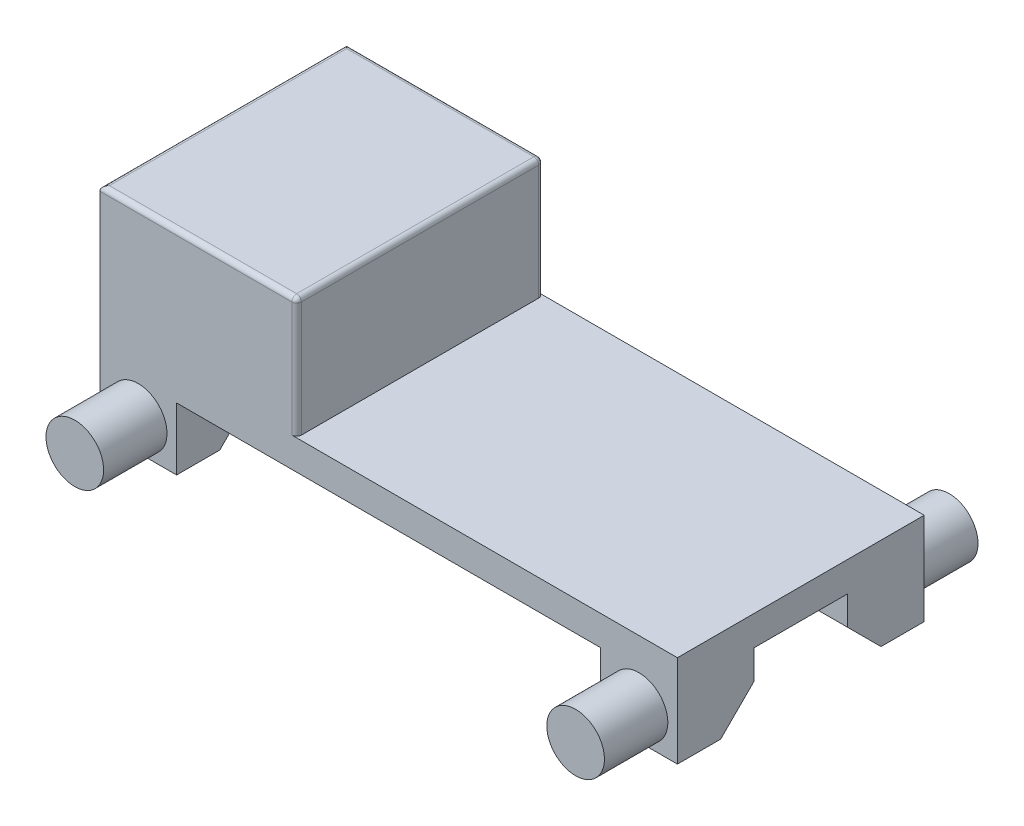
SolidWorks part; units mm, degrees
material "ФФ201"
ref_plane "Спереди" through (0, 0, 0) normal (0, 0, 1) x (1, 0, 0)
ref_plane "Сверху" through (0, 0, 0) normal (0, 1, 0) x (1, 0, 0)
ref_plane "Справа" through (0, 0, 0) normal (1, 0, 0) x (0, 0, -1)
sketch "Эскиз1" plane through (0, 0, 0) normal (0, 1, 0) x (1, 0, 0)
  line L1 (-601.5, -257) -> (601.5, -257)
  line L2 (-601.5, -257) -> (-601.5, 257)
  line L3 (-601.5, 257) -> (601.5, 257)
  line L4 (601.5, -257) -> (601.5, 257)
  line L5 (-601.5, -257) -> (601.5, 257) construction
  line L6 (-601.5, 257) -> (601.5, -257) construction
  point P0 (0, 0)
  dimension "D1" = 1203
  dimension "D2" = 514
extrude "Бобышка-Вытянуть1" add sketch "Эскиз1" along normal blind 62
sketch "Эскиз2" plane through (0, 62, 0) normal (0, 1, 0) x (1, 0, 0)
  line L0 (-601.5, -257) -> (601.5, -257) construction
  line L1 (-601.5, 257) -> (-191.5, 257)
  line L2 (-601.5, 257) -> (-601.5, -257)
  line L3 (-601.5, -257) -> (-191.5, -257)
  line L4 (-191.5, 257) -> (-191.5, -257)
  dimension "D1" = 410
extrude "Бобышка-Вытянуть2" add sketch "Эскиз2" along normal blind 250
fillet "Скругление1" radius 10 6 edges at (-191.5, 187, -257) (-191.5, 187, 257) (-191.5, 312, 0) (-396.5, 312, -257) (-601.5, 312, 0) (-396.5, 312, 257)
sketch "Эскиз3" plane through (0, 0, 0) normal (0, -1, 0) x (1, 0, 0)
  line L0 (171.6, 0) -> (-171.6, 0) construction
  line L1 (-601.5, 257) -> (-441.5, 257)
  line L2 (-601.5, 257) -> (-601.5, 97)
  line L3 (-601.5, 97) -> (-441.5, 97)
  line L4 (-441.5, 257) -> (-441.5, 97)
  line L5 (-601.5, -97) -> (-441.5, -97)
  line L6 (-441.5, -257) -> (-441.5, -97)
  line L7 (-601.5, -257) -> (-441.5, -257)
  line L8 (-601.5, -257) -> (-601.5, -97)
  line L9 (0, -171.6) -> (0, 171.6) construction
  line L10 (601.5, -257) -> (601.5, -97)
  line L11 (601.5, -257) -> (441.5, -257)
  line L12 (441.5, -257) -> (441.5, -97)
  line L13 (601.5, -97) -> (441.5, -97)
  line L14 (601.5, 97) -> (441.5, 97)
  line L15 (441.5, 257) -> (441.5, 97)
  line L16 (601.5, 257) -> (441.5, 257)
  line L17 (601.5, 257) -> (601.5, 97)
  dimension "D1" = 160
  dimension "D2" = 160
extrude "Бобышка-Вытянуть3" add sketch "Эскиз3" along normal blind 130
sketch "Эскиз4" plane through (0, 0, 257) normal (0, 0, 1) x (1, 0, 0)
  line L0 (-441.5, 0) -> (-601.5, 0) construction
  line L1 (-601.5, 302) -> (-601.5, -130) construction
  line L2 (-441.5, 0) -> (-601.5, -130) construction
  line L3 (-601.5, -130) -> (-601.5, 0) construction
  line L4 (-601.5, 0) -> (-441.5, -130) construction
  line L5 (0, -243.1) -> (0, 243.1) construction
  circle A0 centre (-521.5, -65) radius 60
  circle A1 centre (521.5, -65) radius 60
  dimension "D1" = 120
sketch "Эскиз5" plane through (0, 0, -257) normal (0, 0, -1) x (-1, 0, 0)
  line L0 (0, 243.1) -> (0, -243.1) construction
  circle A0 centre (521.5, -65) radius 60
  circle A1 centre (-521.5, -65) radius 60
chamfer "Фаска1" distance 70 angle 45 4 edges at (-521.5, -130, 97) (-521.5, -130, -97) (521.5, -130, -97) (521.5, -130, 97)
extrude "Бобышка-Вытянуть4" add sketch "Эскиз5" along normal blind 132 contours A1 | A0
extrude "Бобышка-Вытянуть5" add sketch "Эскиз4" along normal blind 132 contours A0 | A1
